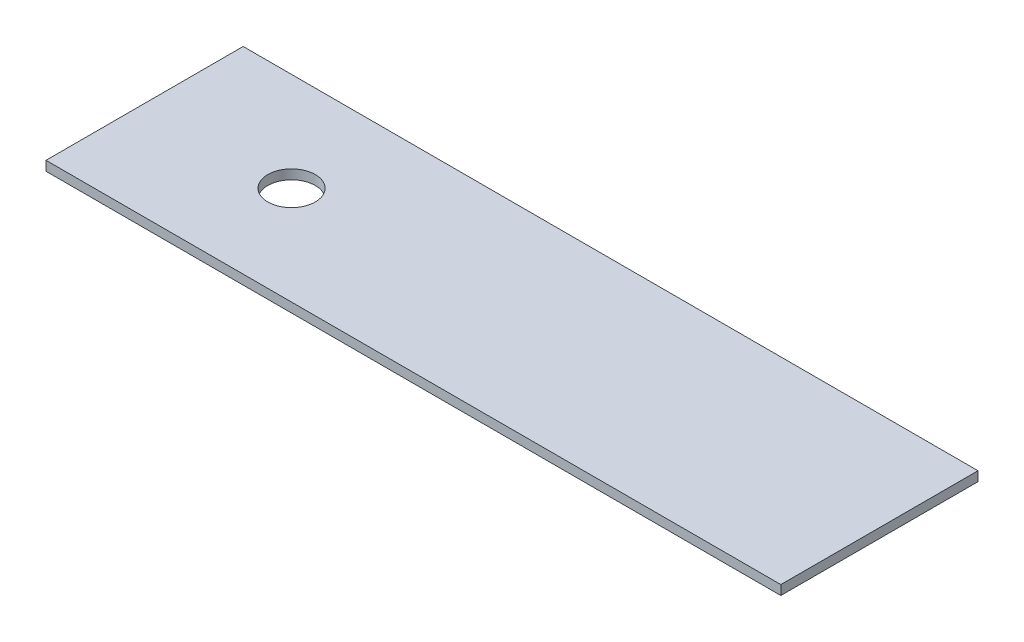
SolidWorks part; units mm, degrees
ref_plane "Front Plane" through (0, 0, 0) normal (0, 0, 1) x (1, 0, 0)
ref_plane "Top Plane" through (0, 0, 0) normal (0, 1, 0) x (1, 0, 0)
ref_plane "Right Plane" through (0, 0, 0) normal (1, 0, 0) x (0, 0, -1)
sketch "Sketch1" plane through (0, 0, 0) normal (0, 1, 0) x (1, 0, 0)
  line L0 (0, 0) -> (-46.4, 0) construction
  line L1 (232, -62.25) -> (-232, -62.25)
  line L2 (232, -62.25) -> (232, 62.25)
  line L3 (232, 62.25) -> (-232, 62.25)
  line L4 (-232, -62.25) -> (-232, 62.25)
  line L5 (232, -62.25) -> (-232, 62.25) construction
  line L6 (232, 62.25) -> (-232, -62.25) construction
  line L7 (-46.4, 0) -> (-92.8, 0) construction
  line L8 (-92.8, 0) -> (-139.2, 0) construction
  line L9 (-139.2, 0) -> (-185.6, 0) construction
  line L10 (-185.6, 0) -> (-232, 0) construction
  circle A0 centre (-139.2, 0) radius 15
  point P0 (0, 0)
  dimension "D2" = 30
  dimension "D1" = 124.5
  dimension "D3" = 464
extrude "Boss-Extrude1" add sketch "Sketch1" along normal blind 6
